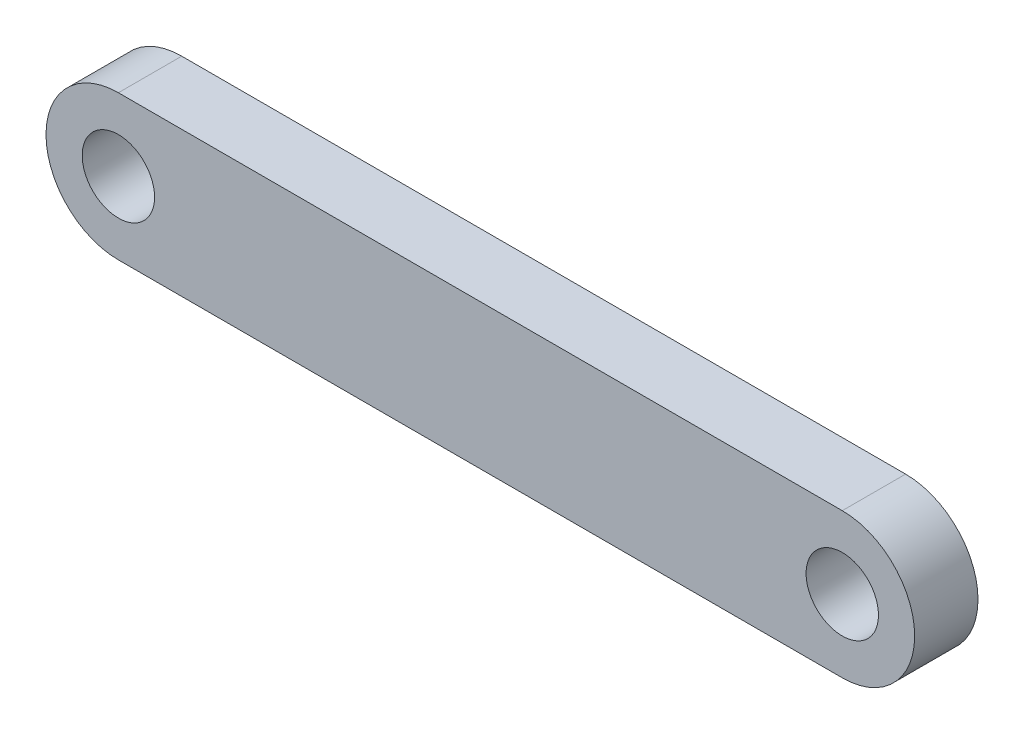
SolidWorks part; units mm, degrees
ref_plane "Piano frontale" through (0, 0, 0) normal (0, 0, 1) x (1, 0, 0)
ref_plane "Piano superiore" through (0, 0, 0) normal (0, 1, 0) x (1, 0, 0)
ref_plane "Piano destro" through (0, 0, 0) normal (1, 0, 0) x (0, 0, -1)
sketch "Schizzo1" plane through (0, 0, 0) normal (0, 0, 1) x (1, 0, 0)
  line L0 (0, 0) -> (100, 0) construction
  line L1 (0, 0) -> (100, 0) construction
  line L2 (0, 10) -> (100, 10)
  line L3 (0, -10) -> (100, -10)
  arc A0 (0, 10) -> (0, -10) centre (0, 0) ccw
  arc A1 (100, -10) -> (100, 10) centre (100, 0) ccw
  circle A2 centre (0, 0) radius 5
  circle A3 centre (100, 0) radius 5
  point P3 (50, 0)
  dimension "D2" = 10
  dimension "D3" = 10
  dimension "D1" = 100
extrude "Estrusione-Estrusione1" add sketch "Schizzo1" along normal blind 8.75
